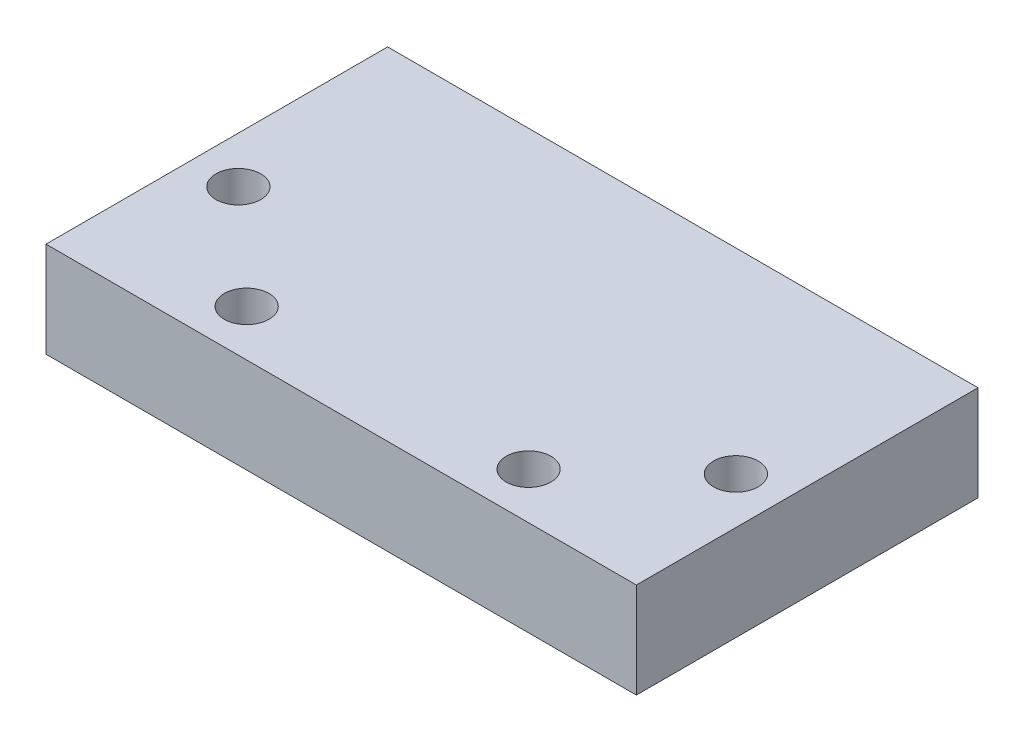
SolidWorks part; units mm, degrees
ref_plane "Front Plane" through (0, 0, 0) normal (0, 0, 1) x (1, 0, 0)
ref_plane "Top Plane" through (0, 0, 0) normal (0, 1, 0) x (1, 0, 0)
ref_plane "Right Plane" through (0, 0, 0) normal (1, 0, 0) x (0, 0, -1)
sketch "Sketch1" plane through (0, 0, 0) normal (0, 0, 1) x (1, 0, 0)
  line L0 (-17.8, 5.75) -> (17.8, 5.75)
  line L1 (17.8, 5.75) -> (17.8, 0)
  line L2 (17.8, 0) -> (12.2, 0)
  line L3 (12.2, 0) -> (12.2, 2.75)
  line L4 (12.2, 2.75) -> (-12.2, 2.75)
  line L5 (-12.2, 2.75) -> (-12.2, 0)
  line L6 (-12.2, 0) -> (-17.8, 0)
  line L7 (-17.8, 0) -> (-17.8, 5.75)
  line L8 (-12.2, 0) -> (12.2, 0) construction
  dimension "D1" = 35.6
  dimension "D2" = 24.4
  dimension "D3" = 3
  dimension "D4" = 2.75
extrude "Boss-Extrude1" add sketch "Sketch1" along normal mid plane 15
sketch "Sketch8" plane through (0, 0, 7.5) normal (0, 0, 1) x (1, 0, 0)
  line L1 (-17.8, 0) -> (17.8, 0)
  line L2 (-17.8, 0) -> (-17.8, 5.75)
  line L3 (-17.8, 5.75) -> (17.8, 5.75)
  line L4 (17.8, 0) -> (17.8, 5.75)
  line L5 (-17.8, 0) -> (17.8, 5.75) construction
  line L6 (-17.8, 5.75) -> (17.8, 0) construction
  point P0 (0, 2.875)
extrude "Boss-Extrude4" add sketch "Sketch8" along normal blind 5.6
sketch "Sketch9" plane through (0, 5.75, 0) normal (0, 1, 0) x (1, 0, 0)
  line L0 (17.8, -13.1) -> (-17.8, -13.1) construction
  line L1 (-17.8, -13.1) -> (-17.8, 7.5) construction
  line L2 (15, -4.3) -> (-15, -4.3) construction
  line L3 (8.5, -10.3) -> (-8.5, -10.3) construction
  line L4 (0, 0) -> (0, -4.3) construction
  line L5 (0, -4.3) -> (0, -10.3) construction
  circle A0 centre (-8.5, -10.3) radius 1.35
  circle A1 centre (-15, -4.3) radius 1.35
  circle A2 centre (8.5, -10.3) radius 1.35
  circle A3 centre (15, -4.3) radius 1.35
  dimension "D1" = 2.7
  dimension "D2" = 2.8
  dimension "D3" = 2.8
  dimension "D4" = 17
  dimension "D5" = 6
extrude "Cut-Extrude3" cut sketch "Sketch9" against normal through all
